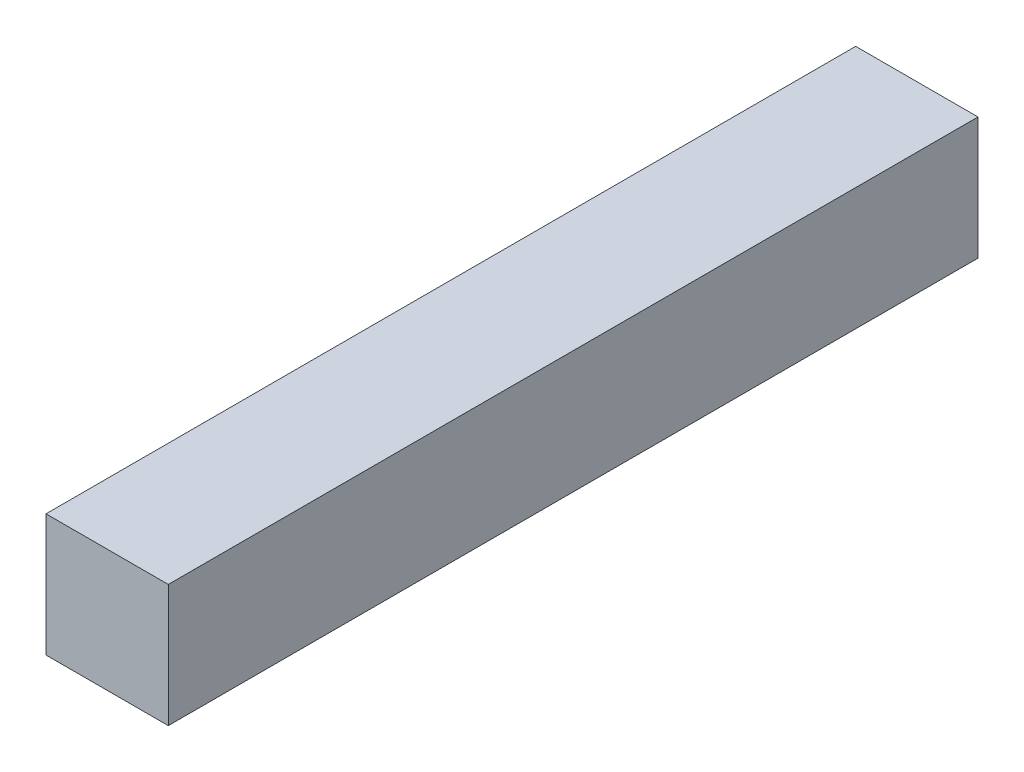
SolidWorks part; units mm, degrees
ref_plane "Plan de face" through (0, 0, 0) normal (0, 0, 1) x (1, 0, 0)
ref_plane "Plan de dessus" through (0, 0, 0) normal (0, 1, 0) x (1, 0, 0)
ref_plane "Plan de droite" through (0, 0, 0) normal (1, 0, 0) x (0, 0, -1)
sketch "Esquisse1" plane through (0, 0, 0) normal (0, 0, 1) x (1, 0, 0)
  line L0 (-5, 5) -> (5, -5) construction
  line L1 (-5, 5) -> (5, 5)
  line L2 (-5, 5) -> (-5, -5)
  line L3 (-5, -5) -> (5, -5)
  line L4 (5, 5) -> (5, -5)
  dimension "D1" = 10
extrude "Boss.-Extru.1" add sketch "Esquisse1" along normal offset from surface (66.2 mm away) 2
